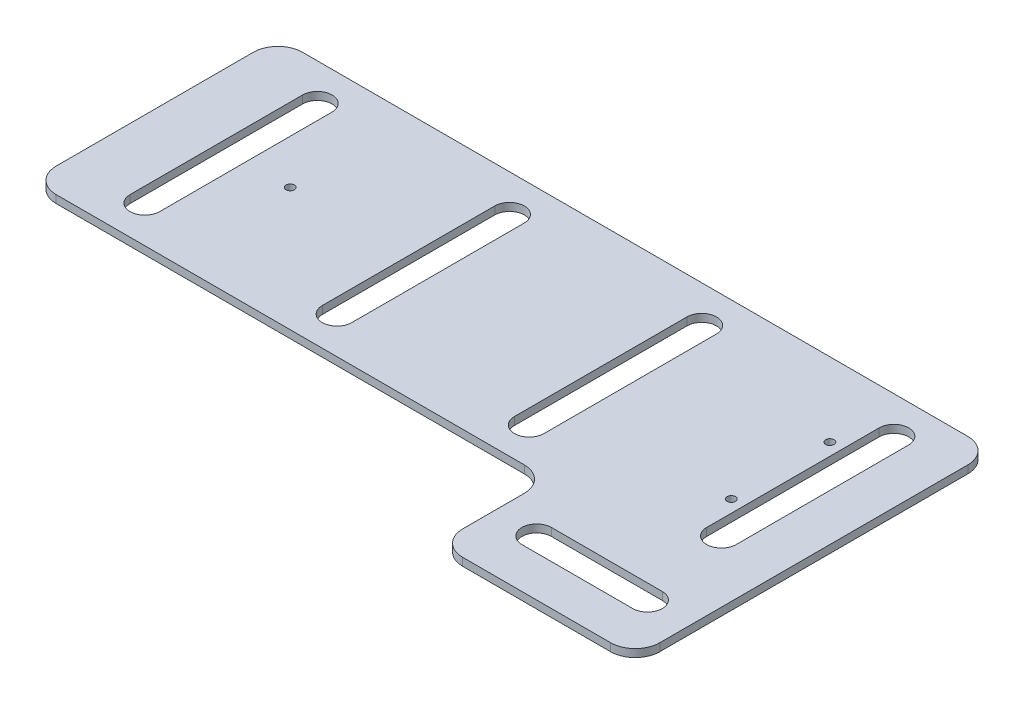
SolidWorks part; units mm, degrees
ref_plane "Front Plane" through (0, 0, 0) normal (0, 0, 1) x (1, 0, 0)
ref_plane "Top Plane" through (0, 0, 0) normal (0, 1, 0) x (1, 0, 0)
ref_plane "Right Plane" through (0, 0, 0) normal (1, 0, 0) x (0, 0, -1)
sketch "Sketch1" plane through (0, 0, 0) normal (0, 1, 0) x (1, 0, 0)
  line L0 (65, -50) -> (145, -50) construction
  line L1 (65, -50) -> (37.5, -50)
  line L2 (145, -50) -> (145, 50)
  line L3 (145, 50) -> (-145, 50)
  line L4 (-145, -50) -> (-145, 50)
  line L5 (145, -50) -> (-145, 50) construction
  line L6 (145, 50) -> (-145, -50) construction
  line L8 (145, -50) -> (145, -95)
  line L9 (145, -95) -> (65, -95)
  line L10 (65, -50) -> (65, -95)
  line L11 (-37.5, -50) -> (-145, -50)
  line L13 (-37.5, -50) -> (-37.5, -85)
  line L14 (-37.5, -85) -> (37.5, -85)
  line L15 (37.5, -50) -> (37.5, -85)
  line L16 (0, 85) -> (0, -85) construction
  line L17 (-37.5, -50) -> (37.5, -50)
  circle A0 centre (28.194, -67.06) radius 1.75
  circle A1 centre (-28.194, -67.06) radius 1.75
  point P0 (0, 0)
  point P13 (0, -85)
  point P21 (0, 0)
  dimension "D8" = 3.5
  dimension "D1" = 290
  dimension "D2" = 100
  dimension "D3" = 45
  dimension "D4" = 80
  dimension "D5" = 75
  dimension "D6" = 35
  dimension "D7" = 17.94
  dimension "D9" = 9.306
extrude "Boss-Extrude1" add sketch "Sketch1" along normal blind 3.175 contours L11 L17 L1 L10 L9 L8 L2 L3 L4
fillet "Fillet1" radius 10 6 edges at (145, 1.5875, -50) (145, 1.5875, 95) (65, 1.5875, 95) (65, 1.5875, 50) (-145, 1.5875, -50) (-145, 1.5875, 50)
sketch "Sketch2" plane through (0, 3.175, 0) normal (0, 1, 0) x (1, 0, 0)
  point P1 (0, 0)
  point P2 (0, 0)
  point P4 (109, 20)
  point P5 (109, -20)
  point P7 (0, 0)
  point P8 (-90, 0)
  point P10 (0, 0)
hole_wizard "standoff holes" positions "Sketch3" profile "Sketch4" hole size "M3" standard "ANSI Metric" end condition through all
sketch "Sketch3" plane through (0, 3.175, 0) normal (0, 1, 0) x (1, 0, 0)
  point P0 (-90, 0)
  point P3 (109, 20)
  point P6 (109, -20)
sketch "Sketch4" plane through (-90, 3.175, 0) normal (1, 0, 0) x (0, 0, 1)
  line L0 (0, 0) -> (0, 3.175)
  line L1 (0, 3.175) -> (1.7, 3.175)
  line L2 (1.7, 3.175) -> (1.7, 0)
  line L5 (1.7, 0) -> (0, 0)
  line L11 (0, -6.35) -> (0, 107.95) construction
  dimension "Thru Hole Dia." = 3.4
  dimension "Thru Hole Depth" = 3.175
sketch "Sketch6" plane through (0, 3.175, 0) normal (0, 1, 0) x (1, 0, 0)
  line L0 (-114, 35) -> (-114, -35) construction
  line L1 (-108, 35) -> (-108, -35)
  line L2 (-120, 35) -> (-120, -35)
  line L3 (-145, -40) -> (-145, 40) construction
  line L4 (-36, 35) -> (-36, -35) construction
  line L5 (-30, 35) -> (-30, -35)
  line L6 (-42, 35) -> (-42, -35)
  line L7 (42, 35) -> (42, -35) construction
  line L8 (48, 35) -> (48, -35)
  line L9 (36, 35) -> (36, -35)
  line L10 (120, 35) -> (120, -35) construction
  line L11 (126, 35) -> (126, -35)
  line L12 (114, 35) -> (114, -35)
  line L22 (82.5, -72.5) -> (127.5, -72.5) construction
  line L23 (82.5, -66.5) -> (127.5, -66.5)
  line L24 (82.5, -78.5) -> (127.5, -78.5)
  line L25 (135, -95) -> (75, -95) construction
  line L26 (65, -60) -> (65, -85) construction
  arc A0 (-108, 35) -> (-120, 35) centre (-114, 35) ccw
  arc A1 (-120, -35) -> (-108, -35) centre (-114, -35) ccw
  arc A2 (-30, 35) -> (-42, 35) centre (-36, 35) ccw
  arc A3 (-42, -35) -> (-30, -35) centre (-36, -35) ccw
  arc A4 (48, 35) -> (36, 35) centre (42, 35) ccw
  arc A5 (36, -35) -> (48, -35) centre (42, -35) ccw
  arc A6 (126, 35) -> (114, 35) centre (120, 35) ccw
  arc A7 (114, -35) -> (126, -35) centre (120, -35) ccw
  arc A14 (82.5, -66.5) -> (82.5, -78.5) centre (82.5, -72.5) ccw
  arc A15 (127.5, -78.5) -> (127.5, -66.5) centre (127.5, -72.5) ccw
  point P2 (-114, 0)
  point P11 (-145, 0)
  point P14 (-36, 0)
  point P21 (42, 0)
  point P28 (120, 0)
  point P54 (105, -72.5)
  point P61 (105, -95)
  point P64 (65, -72.5)
  dimension "D1" = 6
  dimension "D2" = 70
  dimension "D3" = 25
  dimension "D5" = 78
  dimension "D6" = 45
  dimension "D4" = 4
extrude "Cut-Extrude1" cut sketch "Sketch6" against normal up to surface (3.175 mm away) up to face at (-90, 0, 1.7)
